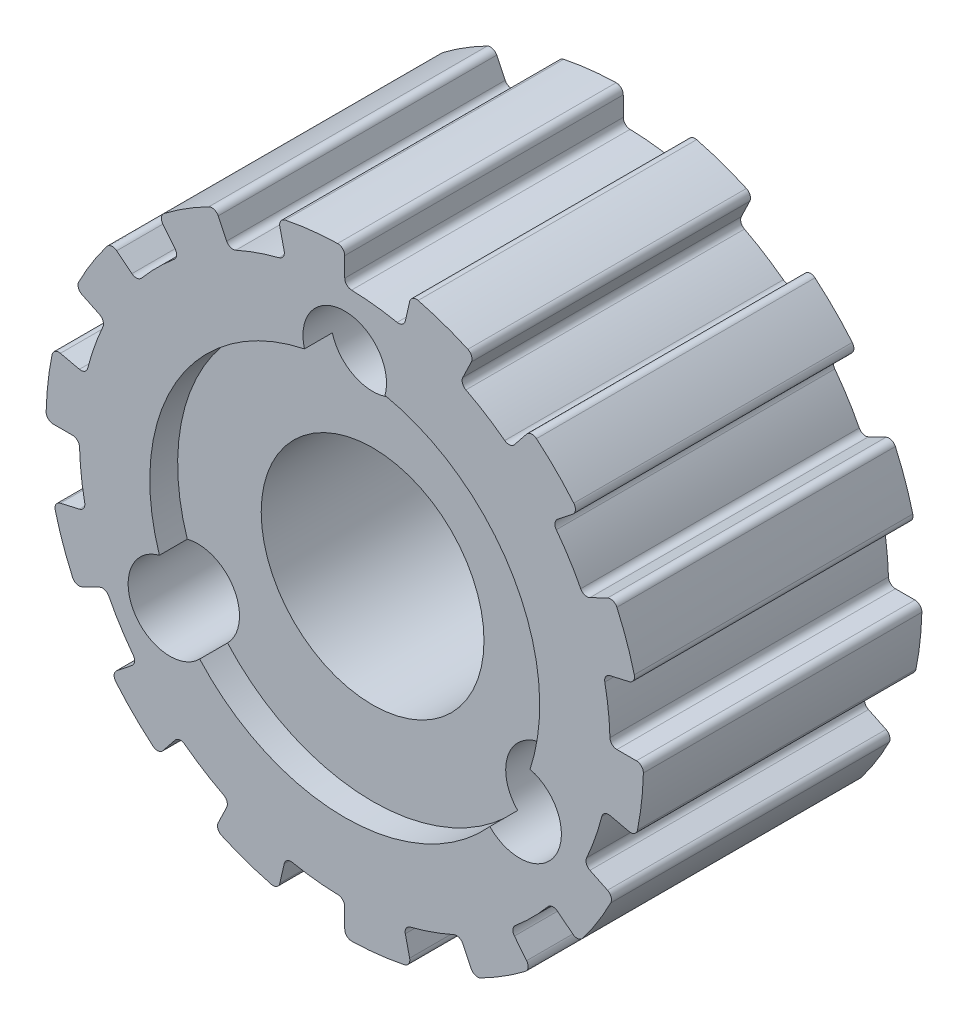
SolidWorks part; units mm, degrees
ref_plane "Plan de face" through (0, 0, 0) normal (0, 0, 1) x (1, 0, 0)
ref_plane "Plan de dessus" through (0, 0, 0) normal (0, 1, 0) x (1, 0, 0)
ref_plane "Plan de droite" through (0, 0, 0) normal (1, 0, 0) x (0, 0, -1)
sketch "Esquisse1" plane through (0, 0, 0) normal (0, 0, 1) x (1, 0, 0)
  line L0 (4.2398, 8.8041) -> (4.5436, 9.435)
  line L1 (6.0926, 7.6399) -> (6.5292, 8.1874)
  line L2 (7.6399, 6.0926) -> (8.1874, 6.5292)
  line L3 (8.8041, 4.2398) -> (9.435, 4.5436)
  line L4 (9.5268, 2.1744) -> (10.2095, 2.3302)
  line L5 (9.7718, 0) -> (10.472, 0)
  line L6 (9.5268, -2.1744) -> (10.2095, -2.3302)
  line L7 (8.8041, -4.2398) -> (9.435, -4.5436)
  line L8 (7.6399, -6.0926) -> (8.1874, -6.5292)
  line L9 (6.0926, -7.6399) -> (6.5292, -8.1874)
  line L10 (4.2398, -8.8041) -> (4.5436, -9.435)
  line L11 (2.1744, -9.5268) -> (2.3302, -10.2095)
  line L12 (0, -9.7718) -> (0, -10.472)
  line L13 (-2.1744, -9.5268) -> (-2.3302, -10.2095)
  line L14 (-4.2398, -8.8041) -> (-4.5436, -9.435)
  line L15 (-6.0926, -7.6399) -> (-6.5292, -8.1874)
  line L16 (-7.6399, -6.0926) -> (-8.1874, -6.5292)
  line L17 (-8.8041, -4.2398) -> (-9.435, -4.5436)
  line L18 (-9.5268, -2.1744) -> (-10.2095, -2.3302)
  line L19 (-9.7718, 0) -> (-10.472, 0)
  line L20 (-9.5268, 2.1744) -> (-10.2095, 2.3302)
  line L21 (-8.8041, 4.2398) -> (-9.435, 4.5436)
  line L22 (-7.6399, 6.0926) -> (-8.1874, 6.5292)
  line L23 (-6.0926, 7.6399) -> (-6.5292, 8.1874)
  line L24 (-4.2398, 8.8041) -> (-4.5436, 9.435)
  line L25 (-2.1744, 9.5268) -> (-2.3302, 10.2095)
  line L29 (0, 9.7718) -> (0, 10.472)
  line L30 (2.1744, 9.5268) -> (2.3302, 10.2095)
  arc A0 (5.7463, 7.5964) -> (4.3509, 8.4732) centre (0, 0) ccw
  circle A1 centre (0, 0) radius 4
  arc A2 (5.7463, 7.5964) -> (6.0926, 7.6399) centre (5.8972, 7.7958) ccw
  arc A3 (1.8813, 9.3374) -> (0.2436, 9.5219) centre (0, 0) ccw
  arc A4 (1.8813, 9.3374) -> (2.1744, 9.5268) centre (1.9307, 9.5824) ccw
  arc A5 (4.4215, 9.7712) -> (2.6354, 10.3962) centre (0, 0) ccw
  arc A6 (8.2232, 6.8851) -> (6.8851, 8.2232) centre (0, 0) ccw
  arc A7 (2.3302, 10.2095) -> (2.6354, 10.3962) centre (2.574, 10.1538) cw
  arc A8 (6.5292, 8.1874) -> (6.8851, 8.2232) centre (6.7247, 8.0315) cw
  arc A9 (4.3509, 8.4732) -> (4.2398, 8.8041) centre (4.4651, 8.6956) cw
  arc A10 (0.2436, 9.5219) -> (0, 9.7718) centre (0.25, 9.7718) cw
  arc A11 (0, 10.472) -> (-0.256, 10.7219) centre (-0.25, 10.472) ccw
  arc A12 (4.5436, 9.435) -> (4.4215, 9.7712) centre (4.3184, 9.5434) ccw
  arc A13 (8.4732, 4.3509) -> (7.5964, 5.7463) centre (0, 0) ccw
  arc A14 (8.4732, 4.3509) -> (8.8041, 4.2398) centre (8.6956, 4.4651) ccw
  arc A15 (10.3962, 2.6354) -> (9.7712, 4.4215) centre (0, 0) ccw
  arc A16 (9.435, 4.5436) -> (9.7712, 4.4215) centre (9.5434, 4.3184) cw
  arc A17 (7.5964, 5.7463) -> (7.6399, 6.0926) centre (7.7958, 5.8972) cw
  arc A18 (8.1874, 6.5292) -> (8.2232, 6.8851) centre (8.0315, 6.7247) ccw
  arc A19 (9.5219, 0.2436) -> (9.3374, 1.8813) centre (0, 0) ccw
  arc A20 (9.5219, 0.2436) -> (9.7718, 0) centre (9.7718, 0.25) ccw
  arc A21 (10.5101, -2.1363) -> (10.7219, -0.256) centre (0, 0) ccw
  arc A22 (10.472, 0) -> (10.7219, -0.256) centre (10.472, -0.25) cw
  arc A23 (9.3374, 1.8813) -> (9.5268, 2.1744) centre (9.5824, 1.9307) cw
  arc A24 (10.2095, 2.3302) -> (10.3962, 2.6354) centre (10.1538, 2.574) ccw
  arc A25 (8.6846, -3.9119) -> (9.2289, -2.3563) centre (0, 0) ccw
  arc A26 (8.6846, -3.9119) -> (8.8041, -4.2398) centre (8.9126, -4.0146) ccw
  arc A27 (8.5423, -6.4849) -> (9.5491, -4.8827) centre (0, 0) ccw
  arc A28 (9.435, -4.5436) -> (9.5491, -4.8827) centre (9.3265, -4.7689) cw
  arc A29 (9.2289, -2.3563) -> (9.5268, -2.1744) centre (9.4712, -2.4182) cw
  arc A30 (10.2095, -2.3302) -> (10.5101, -2.1363) centre (10.2651, -2.0865) ccw
  arc A31 (6.1273, -7.2926) -> (7.2926, -6.1273) centre (0, 0) ccw
  arc A32 (6.1273, -7.2926) -> (6.0926, -7.6399) centre (6.2881, -7.484) ccw
  arc A33 (4.8827, -9.5491) -> (6.4849, -8.5423) centre (0, 0) ccw
  arc A34 (6.5292, -8.1874) -> (6.4849, -8.5423) centre (6.3337, -8.3432) cw
  arc A35 (7.2926, -6.1273) -> (7.6399, -6.0926) centre (7.484, -6.2881) cw
  arc A36 (8.1874, -6.5292) -> (8.5423, -6.4849) centre (8.3432, -6.3337) ccw
  arc A37 (2.3563, -9.2289) -> (3.9119, -8.6846) centre (0, 0) ccw
  arc A38 (2.3563, -9.2289) -> (2.1744, -9.5268) centre (2.4182, -9.4712) ccw
  arc A39 (0.256, -10.7219) -> (2.1363, -10.5101) centre (0, 0) ccw
  arc A40 (2.3302, -10.2095) -> (2.1363, -10.5101) centre (2.0865, -10.2651) cw
  arc A41 (3.9119, -8.6846) -> (4.2398, -8.8041) centre (4.0146, -8.9126) cw
  arc A42 (4.5436, -9.435) -> (4.8827, -9.5491) centre (4.7689, -9.3265) ccw
  arc A43 (-1.8813, -9.3374) -> (-0.2436, -9.5219) centre (0, 0) ccw
  arc A44 (-1.8813, -9.3374) -> (-2.1744, -9.5268) centre (-1.9307, -9.5824) ccw
  arc A45 (-4.4215, -9.7712) -> (-2.6354, -10.3962) centre (0, 0) ccw
  arc A46 (-2.3302, -10.2095) -> (-2.6354, -10.3962) centre (-2.574, -10.1538) cw
  arc A47 (-0.2436, -9.5219) -> (0, -9.7718) centre (-0.25, -9.7718) cw
  arc A48 (0, -10.472) -> (0.256, -10.7219) centre (0.25, -10.472) ccw
  arc A49 (-5.7463, -7.5964) -> (-4.3509, -8.4732) centre (0, 0) ccw
  arc A50 (-5.7463, -7.5964) -> (-6.0926, -7.6399) centre (-5.8972, -7.7958) ccw
  arc A51 (-8.2232, -6.8851) -> (-6.8851, -8.2232) centre (0, 0) ccw
  arc A52 (-6.5292, -8.1874) -> (-6.8851, -8.2232) centre (-6.7247, -8.0315) cw
  arc A53 (-4.3509, -8.4732) -> (-4.2398, -8.8041) centre (-4.4651, -8.6956) cw
  arc A54 (-4.5436, -9.435) -> (-4.4215, -9.7712) centre (-4.3184, -9.5434) ccw
  arc A55 (-8.4732, -4.3509) -> (-7.5964, -5.7463) centre (0, 0) ccw
  arc A56 (-8.4732, -4.3509) -> (-8.8041, -4.2398) centre (-8.6956, -4.4651) ccw
  arc A57 (-10.3962, -2.6354) -> (-9.7712, -4.4215) centre (0, 0) ccw
  arc A58 (-9.435, -4.5436) -> (-9.7712, -4.4215) centre (-9.5434, -4.3184) cw
  arc A59 (-7.5964, -5.7463) -> (-7.6399, -6.0926) centre (-7.7958, -5.8972) cw
  arc A60 (-8.1874, -6.5292) -> (-8.2232, -6.8851) centre (-8.0315, -6.7247) ccw
  arc A61 (-9.5219, -0.2436) -> (-9.3374, -1.8813) centre (0, 0) ccw
  arc A62 (-9.5219, -0.2436) -> (-9.7718, 0) centre (-9.7718, -0.25) ccw
  arc A63 (-10.5101, 2.1363) -> (-10.7219, 0.256) centre (0, 0) ccw
  arc A64 (-10.472, 0) -> (-10.7219, 0.256) centre (-10.472, 0.25) cw
  arc A65 (-9.3374, -1.8813) -> (-9.5268, -2.1744) centre (-9.5824, -1.9307) cw
  arc A66 (-10.2095, -2.3302) -> (-10.3962, -2.6354) centre (-10.1538, -2.574) ccw
  arc A67 (-8.6846, 3.9119) -> (-9.2289, 2.3563) centre (0, 0) ccw
  arc A68 (-8.6846, 3.9119) -> (-8.8041, 4.2398) centre (-8.9126, 4.0146) ccw
  arc A69 (-8.5423, 6.4849) -> (-9.5491, 4.8827) centre (0, 0) ccw
  arc A70 (-9.435, 4.5436) -> (-9.5491, 4.8827) centre (-9.3265, 4.7689) cw
  arc A71 (-9.2289, 2.3563) -> (-9.5268, 2.1744) centre (-9.4712, 2.4182) cw
  arc A72 (-10.2095, 2.3302) -> (-10.5101, 2.1363) centre (-10.2651, 2.0865) ccw
  arc A73 (-6.1273, 7.2926) -> (-7.2926, 6.1273) centre (0, 0) ccw
  arc A74 (-6.1273, 7.2926) -> (-6.0926, 7.6399) centre (-6.2881, 7.484) ccw
  arc A75 (-4.8827, 9.5491) -> (-6.4849, 8.5423) centre (0, 0) ccw
  arc A76 (-6.5292, 8.1874) -> (-6.4849, 8.5423) centre (-6.3337, 8.3432) cw
  arc A77 (-7.2926, 6.1273) -> (-7.6399, 6.0926) centre (-7.484, 6.2881) cw
  arc A78 (-8.1874, 6.5292) -> (-8.5423, 6.4849) centre (-8.3432, 6.3337) ccw
  arc A79 (-2.3563, 9.2289) -> (-3.9119, 8.6846) centre (0, 0) ccw
  arc A80 (-2.3563, 9.2289) -> (-2.1744, 9.5268) centre (-2.4182, 9.4712) ccw
  arc A81 (-0.256, 10.7219) -> (-2.1363, 10.5101) centre (0, 0) ccw
  arc A82 (-2.3302, 10.2095) -> (-2.1363, 10.5101) centre (-2.0865, 10.2651) cw
  arc A83 (-3.9119, 8.6846) -> (-4.2398, 8.8041) centre (-4.0146, 8.9126) cw
  arc A84 (-4.5436, 9.435) -> (-4.8827, 9.5491) centre (-4.7689, 9.3265) ccw
  point P16 (2.1195, 9.2862)
  point P23 (7.4469, 5.9387)
  point P30 (4.6534, 9.6629)
  point P34 (4.1327, 8.5817)
  point P40 (0, 9.525)
  point P46 (0, 10.725)
  point P48 (9.2862, 2.1195)
  point P53 (8.3851, 6.6869)
  point P64 (9.2862, -2.1195)
  point P69 (10.4561, 2.3865)
  point P80 (7.4469, -5.9387)
  point P85 (10.4561, -2.3865)
  point P96 (4.1327, -8.5817)
  point P101 (8.3851, -6.6869)
  point P112 (0, -9.525)
  point P117 (4.6534, -9.6629)
  point P128 (-4.1327, -8.5817)
  point P133 (0, -10.725)
  point P144 (-7.4469, -5.9387)
  point P149 (-4.6534, -9.6629)
  point P160 (-9.2862, -2.1195)
  point P165 (-8.3851, -6.6869)
  point P176 (-9.2862, 2.1195)
  point P181 (-10.4561, -2.3865)
  point P192 (-7.4469, 5.9387)
  point P197 (-10.4561, 2.3865)
  point P208 (-4.1327, 8.5817)
  point P213 (-8.3851, 6.6869)
  point P224 (0, 9.525)
  point P229 (-4.6534, 9.6629)
  dimension "D1" = 0.25
  dimension "D2" = 0.25
  dimension "D5" = 0.25
  dimension "D6" = 0.25
extrude "Extrusion1" add sketch "Esquisse1" along normal blind 10
sketch "Esquisse2" plane through (0, 0, 10) normal (0, 0, 1) x (1, 0, 0)
  circle A0 centre (0, 0) radius 6
sketch "Esquisse3" plane through (0, 0, 10) normal (0, 0, 1) x (1, 0, 0)
  circle A0 centre (0, 0) radius 7
sketch "Esquisse4" plane through (0, 0, 0) normal (0, 0, -1) x (-1, 0, 0)
  circle A1 centre (0, 7.25) radius 1.5
  circle A3 centre (6.2787, -3.625) radius 1.5
  circle A4 centre (-6.2787, -3.625) radius 1.5
extrude "Extrusion4" cut sketch "Esquisse4" against normal through all
extrude "Extrusion6" cut sketch "Esquisse3" against normal blind 1
